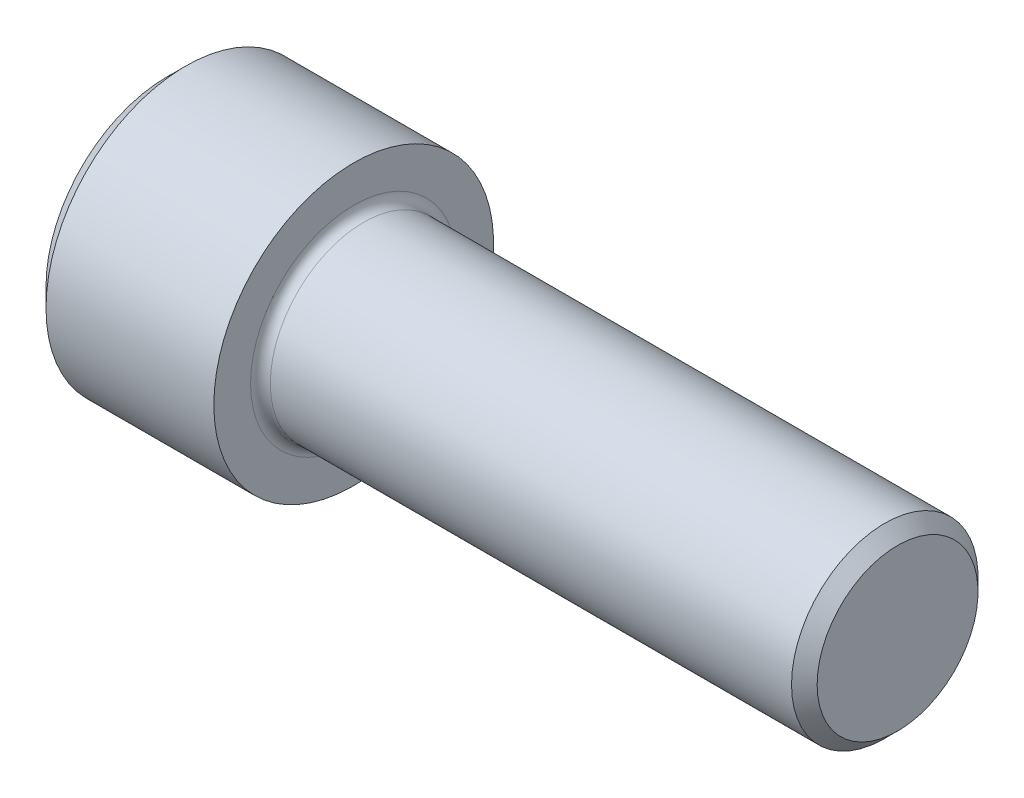
SolidWorks part; units mm, degrees
revolve "Base-Revolve" add sketch "BodySke"
sketch "BodySke" plane through (0, 0, 0) normal (0, 0, 1) x (1, 0, 0)
  line L0 (0, 0) -> (0, 15.6)
  line L1 (2.4, 18) -> (24, 18)
  line L2 (24, 18) -> (24, 12)
  line L3 (24, 12) -> (92.352, 12)
  line L4 (94, 10.352) -> (94, 0)
  line L5 (94, 0) -> (0, 0)
  line L6 (-31.75, 0) -> (127, 0) construction
  line L7 (0, 15.6) -> (2.4, 18)
  line L8 (94, 10.352) -> (92.352, 12)
  line L9 (0, -15.6) -> (2.4, -18) construction
  line L10 (94, -10.352) -> (92.352, -12) construction
  line L11 (27, 9.525) -> (27, 3.175) construction
  line L12 (44, 9.525) -> (44, 3.175) construction
  line L13 (44, 9.525) -> (44, 3.175) construction
  dimension "Diameter" = 24
  dimension "Head_ht" = 24
  dimension "Length" = 70
  dimension "Body_ch_ang" = 45
  dimension "Head_dia" = 36
  dimension "Head_ch_ang" = 45
  dimension "Minor_dia" = 20.704
  dimension "Advance" = 3
  dimension "Thread_nom" = 50
  dimension "Thread_length" = 50
  dimension "Head_ch_ht" = 2.4
cosmetic thread "ThreadCosmetic" [suppressed]
fillet "Fillet1" radius 1.27 1 edges at (24, 0, 12)
ref_plane "Plane1" through (0, 0, 0) normal (0, 0, 1) x (1, 0, 0)
ref_plane "Plane2" through (0, 0, 0) normal (0, 1, 0) x (1, 0, 0)
ref_plane "Plane3" through (0, 0, 0) normal (1, 0, 0) x (0, 0, -1)
sketch "Sketch2" plane through (0, 0, 0) normal (0, 0, 1) x (1, 0, 0)
  line L0 (0, 9.5) -> (12, 9.5)
  line L1 (12, 9.5) -> (17.4848, 0)
  line L2 (-31.75, 0) -> (127, 0) construction
  line L3 (17.4848, 0) -> (0, 0)
  line L4 (0, 0) -> (0, 9.5)
  line L5 (0, 15.6) -> (0, -15.6) construction
  line L6 (0, 0) -> (47.625, 0) construction
  line L7 (24, -18) -> (24, 18) construction
  dimension "D2" = 60
revolve "Hex-PreBroach" cut sketch "Sketch2" angle 360 about L6
sketch "Sketch3" plane through (0, 0, 0) normal (-1, 0, 0) x (0, 0.5, 0.866)
  line L0 (5.4848, 9.5) -> (-5.4848, 9.5)
  line L1 (-5.4848, 9.5) -> (-10.9697, 0)
  line L2 (5.4848, 9.5) -> (10.9697, 0)
  line L3 (5.4848, -9.5) -> (10.9697, 0)
  line L4 (5.4848, -9.5) -> (-5.4848, -9.5)
  line L5 (-5.4848, -9.5) -> (-10.9697, 0)
extrude "Hex" cut sketch "Sketch3" against normal blind 12
sketch "Sketch4" plane through (0, 0, 0) normal (-1, 0, 0) x (0, 0, 1)
  line L0 (0, 0) -> (10.1727, 0)
  line L1 (0, 0) -> (6.1484, 3.5498) construction
  line L2 (0, 0) -> (5.0863, 8.8098)
  line L3 (8.4417, 2.1022) -> (9.7612, 2.864)
  line L4 (6.0414, 6.2596) -> (7.3609, 7.0215)
  arc A0 (8.4417, 2.1022) -> (6.0414, 6.2596) centre (0, 0) ccw
  arc A1 (10.1727, 0) -> (9.7612, 2.864) centre (0, 0) ccw
  arc A2 (5.0863, 8.8098) -> (7.3609, 7.0215) centre (0, 0) cw
  dimension "D1" = 30
  dimension "D2" = 60
extrude "Spline" [suppressed] cut sketch "Sketch4" against normal blind 12.573
pattern_circular "CirPattern1" [suppressed] count 6 every 60
sketch "Sketch5" plane through (0, 0, 0) normal (0, 0, 1) x (1, 0, 0)
  line L0 (-31.75, 0) -> (127, 0) construction
  line L2 (0, 15.6) -> (0, -15.6) construction
  circle A0 centre (7.3, 0) radius 1.075
  dimension "Drilled_hole_dia" = 2.15
  dimension "Drilled_hole_loc" = 7.3
extrude "Hole" [suppressed] cut sketch "Sketch5" against normal through all and the other way through all
pattern_circular "Drilled-4" [suppressed] count 2 every 60
pattern_circular "Drilled-6" [suppressed] count 3 every 60
sketch "ThdSchSke" plane through (0, 0, 0) normal (0, 0, 1) x (1, 0, 0)
  line L0 (44, -10.352) -> (42.8461, -12)
  line L1 (44, -10.352) -> (45.1539, -12)
  line L2 (45.1539, -12) -> (45.1539, -15)
  line L3 (-3.175, 0) -> (5.1513, 0) construction
  line L5 (45.1539, -15) -> (42.8461, -15)
  line L6 (42.8461, -15) -> (42.8461, -12)
  line L7 (0, 15.6) -> (0, -15.6) construction
revolve "ThreadSchematic" [suppressed] cut sketch "ThdSchSke" angle 360 about L3
pattern_linear "ThdSchPat" [suppressed]
equation "\"D2@Sketch3\" = \"Hex_size@Sketch3\" / 2"
equation "\"D1@Sketch3\" = \"Hex_size@Sketch3\" / 2"
equation "\"D1@Sketch2\" = \"Hex_size@Sketch3\" / 2"
equation "\"D3@Sketch4\" = \"Spline_p_dim@Sketch4\" / 2"
equation "\"Thread_minor@ThreadCosmetic\"  =  \"Minor_dia@BodySke\""
equation "\"D2@CirPattern1\" = 360 / \"Num_teeth@CirPattern1\""
equation "\"Wall_thickness@Sketch2\" = \"Head_ht@BodySke\" - \"Key_eng@Hex\""
equation "\"Thread_length@ThreadCosmetic\" = ((sgn( (\"Length@BodySke\" - \"Advance@BodySke\" ) - \"Thread_nom@BodySke\" )-1)*( (\"Length@BodySke\" - \"Advance@BodySke\" ) - \"Thread_nom@BodySke\" ))/-2+ \"Thread_nom@BodySke\""
equation "\"Thread_minor@ThdSchSke\" = \"Minor_dia@BodySke\""
equation "\"Diameter@ThdSchSke\" = \"Diameter@BodySke\""
equation "\"Overcut@ThdSchSke\" = \"Diameter@BodySke\" * 1.25"
equation "\"Start@ThdSchSke\" = \"Head_ht@BodySke\" + \"Length@BodySke\" - \"Thread_length@ThreadCosmetic\"  '---Non-countersunk---"
equation "\"Num_threads@ThdSchPat\" = int( \"Thread_length@ThreadCosmetic\" / \"Advance@BodySke\" + 0.999 )  + 1"
equation "\"Advance@ThdSchPat\" = \"Thread_length@ThreadCosmetic\" /  (\"Num_threads@ThdSchPat\" - 1) 'relax it"
equation "\"Num_threads@ThdSchPat\" = \"Num_threads@ThdSchPat\" - sgn( \"Num_threads@ThdSchPat\" - 1) '---chamfered tips only---"
